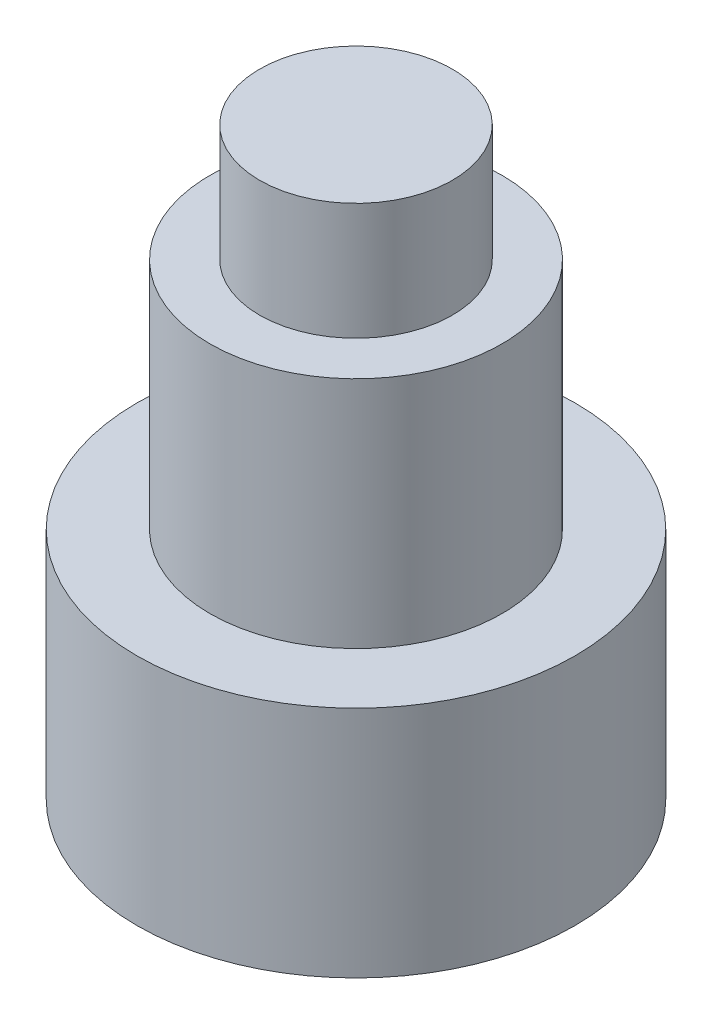
SolidWorks part; units mm, degrees
ref_plane "Front Plane" through (0, 0, 0) normal (0, 0, 1) x (1, 0, 0)
ref_plane "Top Plane" through (0, 0, 0) normal (0, 1, 0) x (1, 0, 0)
ref_plane "Right Plane" through (0, 0, 0) normal (1, 0, 0) x (0, 0, -1)
sketch "Sketch1" plane through (0, 0, 0) normal (0, 1, 0) x (1, 0, 0)
  circle A0 centre (0, 0) radius 3.75
extrude "Boss-Extrude1" add sketch "Sketch1" along normal blind 8
sketch "Sketch2" plane through (0, 8, 0) normal (0, 1, 0) x (1, 0, 0)
  circle A0 centre (0, 0) radius 2.5
  circle A1 centre (0, 0) radius 3.75
extrude "Cut-Extrude1" cut sketch "Sketch2" against normal blind 4
sketch "Sketch3" plane through (0, 8, 0) normal (0, 1, 0) x (1, 0, 0)
  circle A0 centre (0, 0) radius 1.65
extrude "Boss-Extrude2" add sketch "Sketch3" along normal blind 2
